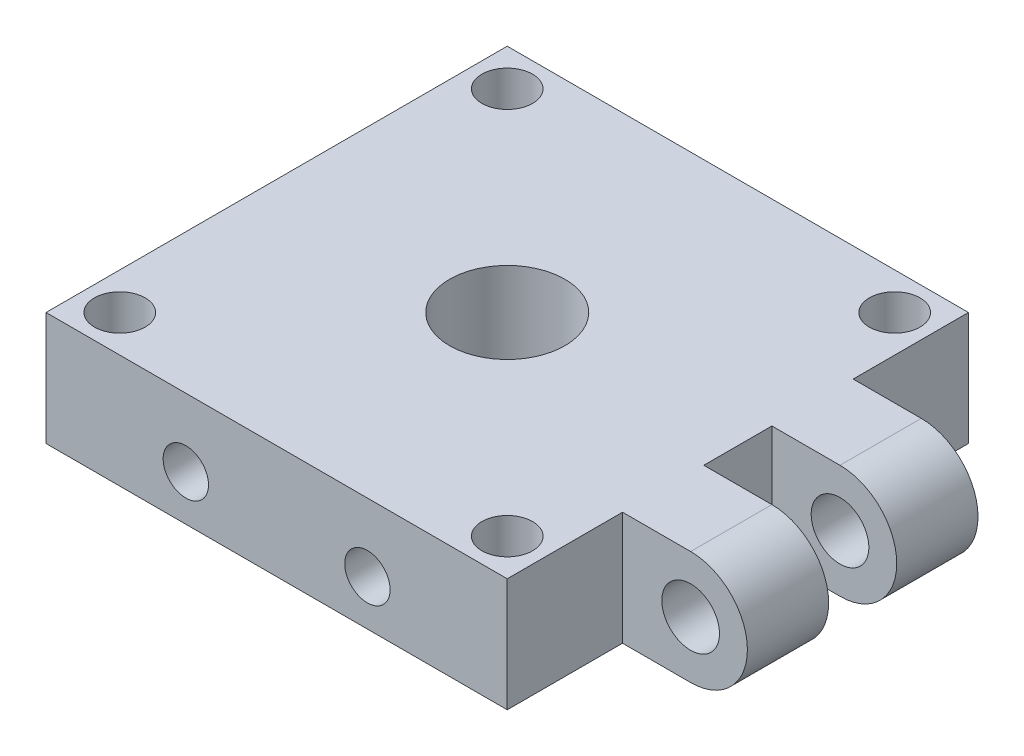
SolidWorks part; units mm, degrees
material "Plain Carbon Steel"
ref_plane "Front Plane" through (0, 0, 0) normal (0, 0, 1) x (1, 0, 0)
ref_plane "Top Plane" through (0, 0, 0) normal (0, 1, 0) x (1, 0, 0)
ref_plane "Right Plane" through (0, 0, 0) normal (1, 0, 0) x (0, 0, -1)
sketch "Sketch1" plane through (0, 0, 0) normal (0, 1, 0) x (1, 0, 0)
  line L1 (-25.4, -25.4) -> (25.4, -25.4)
  line L2 (-25.4, -25.4) -> (-25.4, 25.4)
  line L3 (-25.4, 25.4) -> (25.4, 25.4)
  line L4 (25.4, -25.4) -> (25.4, 25.4)
  line L5 (-25.4, -25.4) -> (25.4, 25.4) construction
  line L6 (-25.4, 25.4) -> (25.4, -25.4) construction
  circle A0 centre (-21.336, -21.336) radius 2.794
  circle A1 centre (21.336, -21.336) radius 2.794
  circle A2 centre (21.336, 21.336) radius 2.794
  circle A3 centre (-21.336, 21.336) radius 2.794
  circle A4 centre (0, 0) radius 6.35
  point P0 (0, 0)
  dimension "D3" = 5.588
  dimension "D4" = 12.7
  dimension "D1" = 50.8
  dimension "D2" = 21.336
extrude "Boss-Extrude1" add sketch "Sketch1" along normal blind 12.5
sketch "Sketch4" plane through (0, 0, 0) normal (0, 0, 1) x (1, 0, 0)
  line L0 (25.4, 12.5) -> (40.4, 12.5) construction
  line L1 (25.4, 0) -> (32.9, 0)
  line L2 (25.4, 0) -> (25.4, 12.5)
  line L3 (25.4, 12.5) -> (32.9, 12.5)
  arc A0 (32.9, 12.5) -> (32.9, 0) centre (32.9, 6.25) cw
  circle A1 centre (32.9, 6.25) radius 3.175
  point P12 (32.9, 12.5)
  dimension "D1" = 6.35
  dimension "D2" = 7.5
extrude "Boss-Extrude2" add sketch "Sketch4" along normal mid plane 25.4
sketch "Sketch5" plane through (0, 12.5, 0) normal (0, 1, 0) x (1, 0, 0)
  line L9 (39.15, -12.7) -> (39.15, 12.7) construction
  line L10 (25.4, 3.75) -> (39.15, 3.75)
  line L11 (25.4, 3.75) -> (25.4, -3.75)
  line L12 (25.4, -3.75) -> (39.15, -3.75)
  line L13 (39.15, 3.75) -> (39.15, -3.75)
  line L14 (25.4, 3.75) -> (39.15, -3.75) construction
  line L15 (25.4, -3.75) -> (39.15, 3.75) construction
  line L16 (25.4, -25.4) -> (25.4, -12.7) construction
  point P0 (32.275, 0)
  dimension "D1" = 7.5
extrude "Cut-Extrude2" cut sketch "Sketch5" against normal through all
sketch "Sketch14" plane through (0, 0, 25.4) normal (0, 0, 1) x (1, 0, 0)
  line L0 (-10, 5) -> (10, 5) construction
  line L1 (-25.4, 0) -> (25.4, 0) construction
  circle A0 centre (-10, 5) radius 2.5
  circle A1 centre (10, 5) radius 2.5
  point P6 (0, 5)
  dimension "D1" = 5
  dimension "D2" = 20
  dimension "D3" = 5
extrude "Cut-Extrude7" cut sketch "Sketch14" against normal blind 20
sketch "Sketch15" plane through (-25.4, 0, 0) normal (-1, 0, 0) x (0, 0, 1)
  line L0 (-10, 5) -> (10, 5) construction
  line L1 (-25.4, 0) -> (25.4, 0) construction
  circle A0 centre (-10, 5) radius 2.5
  circle A1 centre (10, 5) radius 2.5
  point P4 (0, 5)
  dimension "D1" = 5
  dimension "D2" = 20
  dimension "D3" = 5
extrude "Cut-Extrude8" cut sketch "Sketch15" against normal blind 20
